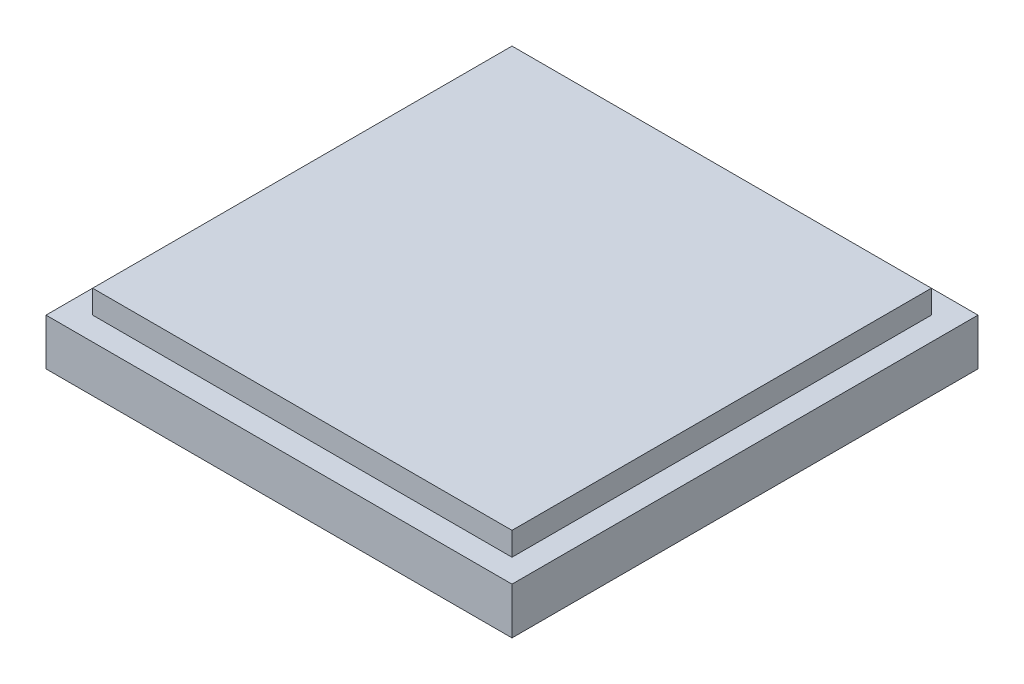
SolidWorks part; units mm, degrees
ref_plane "Alzado" through (0, 0, 0) normal (0, 0, 1) x (1, 0, 0)
ref_plane "Planta" through (0, 0, 0) normal (0, 1, 0) x (1, 0, 0)
ref_plane "Vista lateral" through (0, 0, 0) normal (1, 0, 0) x (0, 0, -1)
sketch "Croquis1" plane through (0, 0, 0) normal (0, 1, 0) x (1, 0, 0)
  line L1 (25, -25) -> (-25, -25)
  line L2 (25, -25) -> (25, 25)
  line L3 (25, 25) -> (-25, 25)
  line L4 (-25, -25) -> (-25, 25)
  line L5 (25, -25) -> (-25, 25) construction
  line L6 (25, 25) -> (-25, -25) construction
  point P0 (0, 0)
  dimension "D1" = 50
  dimension "D2" = 50
extrude "Saliente-Extruir1" add sketch "Croquis1" along normal blind 5
sketch "Croquis2" plane through (0, 5, 0) normal (0, 1, 0) x (1, 0, 0)
  line L1 (22.5, -22.5) -> (-22.5, -22.5)
  line L2 (22.5, -22.5) -> (22.5, 22.5)
  line L3 (22.5, 22.5) -> (-22.5, 22.5)
  line L4 (-22.5, -22.5) -> (-22.5, 22.5)
  line L5 (22.5, -22.5) -> (-22.5, 22.5) construction
  line L6 (22.5, 22.5) -> (-22.5, -22.5) construction
  point P0 (0, 0)
  dimension "D1" = 45
  dimension "D2" = 45
extrude "Saliente-Extruir2" add sketch "Croquis2" along normal blind 2.5
